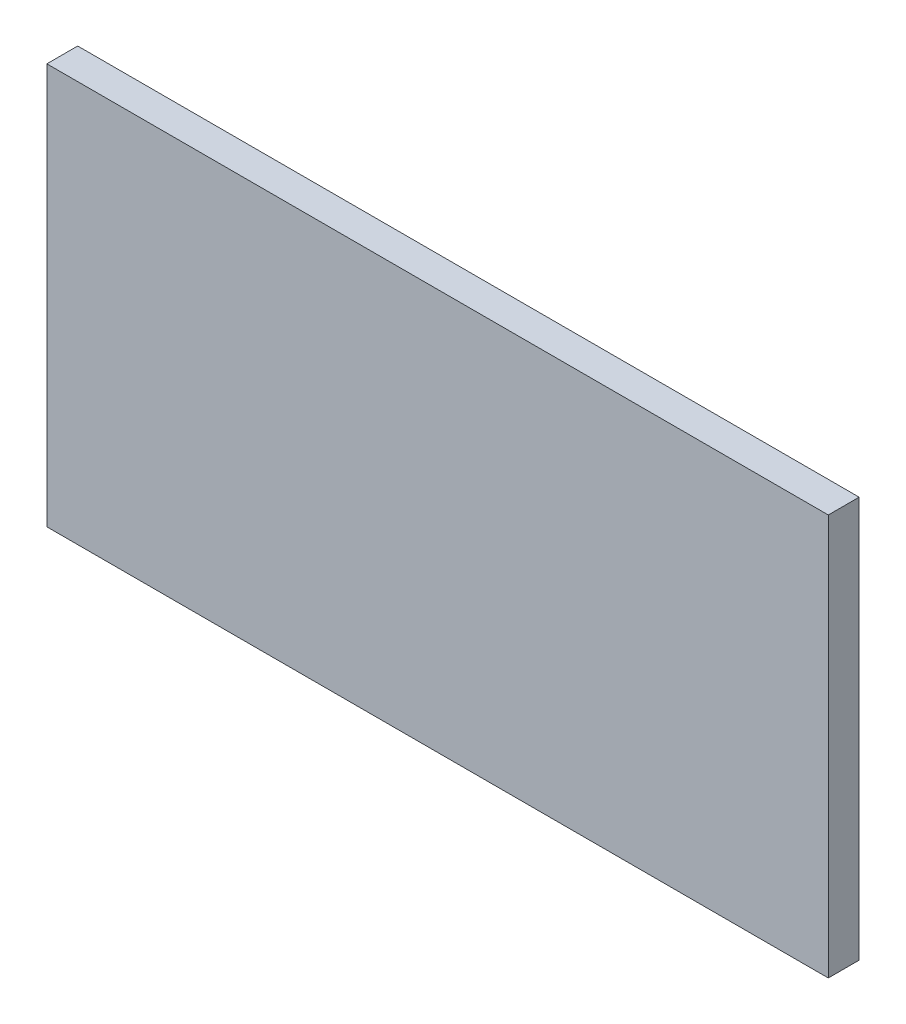
SolidWorks part; units mm, degrees
ref_plane "Front Plane" through (0, 0, 0) normal (0, 0, 1) x (1, 0, 0)
ref_plane "Top Plane" through (0, 0, 0) normal (0, 1, 0) x (1, 0, 0)
ref_plane "Right Plane" through (0, 0, 0) normal (1, 0, 0) x (0, 0, -1)
sketch "Sketch1" plane through (0, 0, 0) normal (0, 0, 1) x (1, 0, 0)
  line L1 (0, 0) -> (76, 0)
  line L2 (0, 0) -> (0, 39)
  line L3 (0, 39) -> (76, 39)
  line L4 (76, 0) -> (76, 39)
  dimension "D1" = 76
  dimension "D2" = 39
extrude "Boss-Extrude1" add sketch "Sketch1" along normal blind 3
